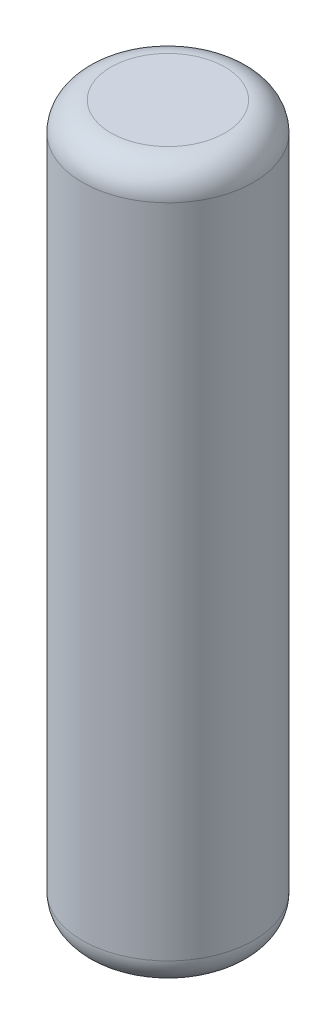
SolidWorks part; units mm, degrees
material "Cast Alloy Steel"
ref_plane "Front Plane" through (0, 0, 0) normal (0, 0, 1) x (1, 0, 0)
ref_plane "Top Plane" through (0, 0, 0) normal (0, 1, 0) x (1, 0, 0)
ref_plane "Right Plane" through (0, 0, 0) normal (1, 0, 0) x (0, 0, -1)
sketch "Sketch1" plane through (0, 0, 0) normal (0, 1, 0) x (1, 0, 0)
  circle A0 centre (0, 0) radius 30
  dimension "D1" = 60
extrude "Boss-Extrude1" add sketch "Sketch1" along normal blind 250
fillet "Fillet1" radius 10 2 edges at (0, 0, 30) (0, 250, 30)
